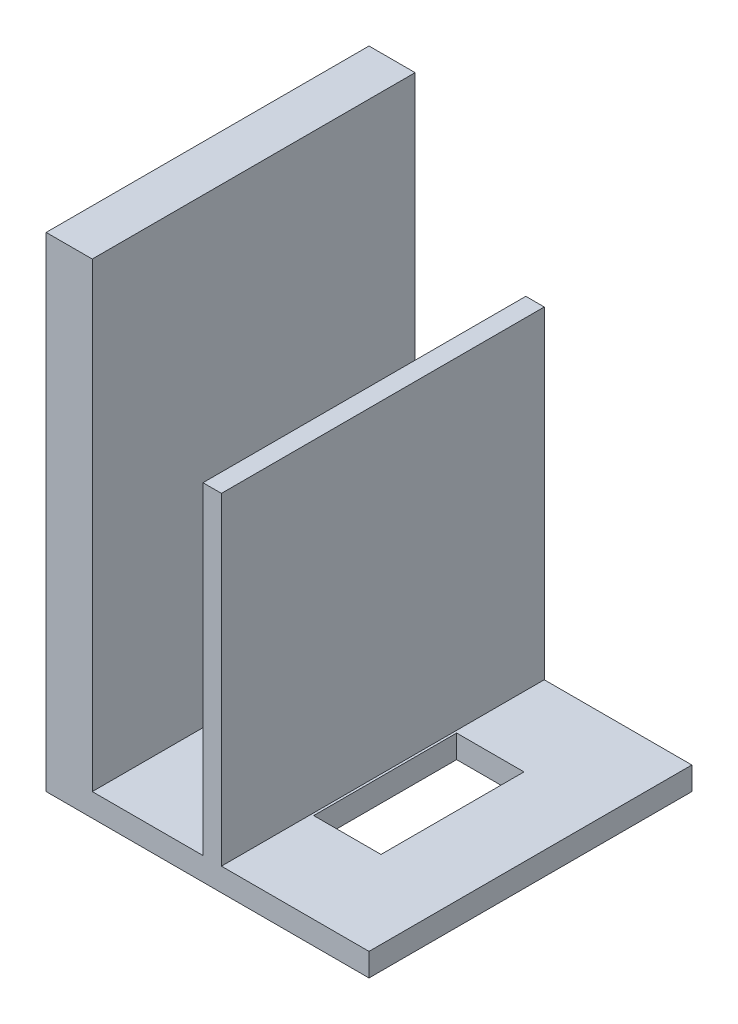
SolidWorks part; units mm, degrees
ref_plane "Front Plane" through (0, 0, 0) normal (0, 0, 1) x (1, 0, 0)
ref_plane "Top Plane" through (0, 0, 0) normal (0, 1, 0) x (1, 0, 0)
ref_plane "Right Plane" through (0, 0, 0) normal (1, 0, 0) x (0, 0, -1)
sketch "Sketch1" plane through (0, 0, 0) normal (0, 1, 0) x (1, 0, 0)
  line L1 (0, 0) -> (35, 0)
  line L2 (0, 0) -> (0, 35)
  line L3 (0, 35) -> (35, 35)
  line L4 (35, 0) -> (35, 35)
  dimension "D1" = 35
  dimension "D2" = 35
extrude "Boss-Extrude1" add sketch "Sketch1" along normal blind 2.5
sketch "Sketch2" plane through (0, 2.5, 0) normal (0, 1, 0) x (1, 0, 0)
  line L0 (0, 0) -> (35, 0) construction
  line L1 (0, 35) -> (5, 35)
  line L2 (0, 35) -> (0, 0)
  line L3 (0, 0) -> (5, 0)
  line L4 (5, 35) -> (5, 0)
  dimension "D1" = 5
extrude "Boss-Extrude2" add sketch "Sketch2" along normal blind 50
sketch "Sketch5" plane through (0, 0, 0) normal (-1, 0, 0) x (0, 0, 1)
  line L0 (-35, 52.5) -> (0, 52.5) construction
  line L1 (-26.0539, 47.5) -> (-9.0539, 47.5)
  line L2 (-26.0539, 47.5) -> (-26.0539, 12.5)
  line L3 (-26.0539, 12.5) -> (-9.0539, 12.5)
  line L4 (-9.0539, 47.5) -> (-9.0539, 12.5)
  dimension "D1" = 17
  dimension "D2" = 35
  dimension "D3" = 5
extrude "Cut-Extrude2" cut sketch "Sketch5" against normal blind 4
sketch "Sketch6" plane through (0, 2.5, 0) normal (0, 1, 0) x (1, 0, 0)
  line L0 (5, 0) -> (5, 35) construction
  line L2 (35, 35) -> (5, 35) construction
  circle A0 centre (10.75, 17.5) radius 5
  dimension "D2" = 10
  dimension "D1" = 5.75
  dimension "D3" = 17.5
extrude "Cut-Extrude3" cut sketch "Sketch6" against normal blind 10
sketch "Sketch7" plane through (0, 2.5, 0) normal (0, 1, 0) x (1, 0, 0)
  line L0 (35, 35) -> (5, 35) construction
  line L1 (17, 0) -> (19, 0)
  line L2 (17, 0) -> (17, 35)
  line L3 (17, 35) -> (19, 35)
  line L4 (19, 0) -> (19, 35)
  line L5 (5, 0) -> (5, 35) construction
  dimension "D1" = 35
  dimension "D2" = 12
  dimension "D3" = 2
extrude "Boss-Extrude3" add sketch "Sketch7" along normal blind 35
sketch "Sketch8" plane through (0, 2.5, 0) normal (0, 1, 0) x (1, 0, 0)
  line L0 (35, 35) -> (19, 35) construction
  line L1 (26.55, 9.75) -> (19.25, 9.75)
  line L2 (26.55, 9.75) -> (26.55, 25.25)
  line L3 (26.55, 25.25) -> (19.25, 25.25)
  line L4 (19.25, 9.75) -> (19.25, 25.25)
  line L5 (19, 0) -> (19, 35) construction
  dimension "D1" = 7.3
  dimension "D2" = 15.5
  dimension "D3" = 9.75
  dimension "D4" = 0.25
extrude "Cut-Extrude4" cut sketch "Sketch8" against normal through all
